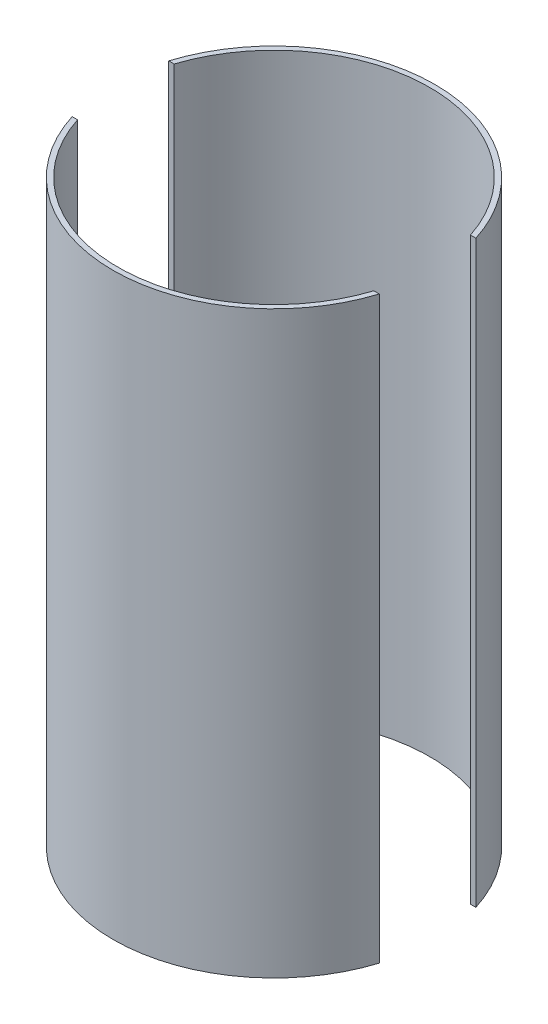
SolidWorks part; units mm, degrees
ref_plane "Front Plane" through (0, 0, 0) normal (0, 0, 1) x (1, 0, 0)
ref_plane "Top Plane" through (0, 0, 0) normal (0, 1, 0) x (1, 0, 0)
ref_plane "Right Plane" through (0, 0, 0) normal (1, 0, 0) x (0, 0, -1)
sketch "Sketch4" plane through (0, 0, 0) normal (0, 1, 0) x (1, 0, 0)
  circle A0 centre (0, 0) radius 63.5
  circle A1 centre (0, 0) radius 61.468
  dimension "D1" = 127
  dimension "D2" = 122.936
extrude "Boss-Extrude1" add sketch "Sketch4" along normal mid plane 228.6
sketch "Sketch5" plane through (0, 0, 0) normal (0, 1, 0) x (1, 0, 0)
  line L1 (-76.2, 19.05) -> (76.2, 19.05)
  line L2 (-76.2, 19.05) -> (-76.2, -19.05)
  line L3 (-76.2, -19.05) -> (76.2, -19.05)
  line L4 (76.2, 19.05) -> (76.2, -19.05)
  line L5 (-76.2, 19.05) -> (76.2, -19.05) construction
  line L6 (-76.2, -19.05) -> (76.2, 19.05) construction
  line L8 (-76.2, -18.415) -> (-76.2, 18.415)
  line L10 (76.2, -18.415) -> (76.2, 18.415)
  line L11 (-76.2, -18.415) -> (76.2, 18.415) construction
  line L12 (-76.2, 18.415) -> (76.2, -18.415) construction
  point P0 (0, 0)
  point P6 (0, 0)
  dimension "D1" = 38.1
  dimension "D2" = 152.4
  dimension "D3" = 152.4
extrude "Cut-Extrude2" cut sketch "Sketch5" against normal through all both and the other way through all
